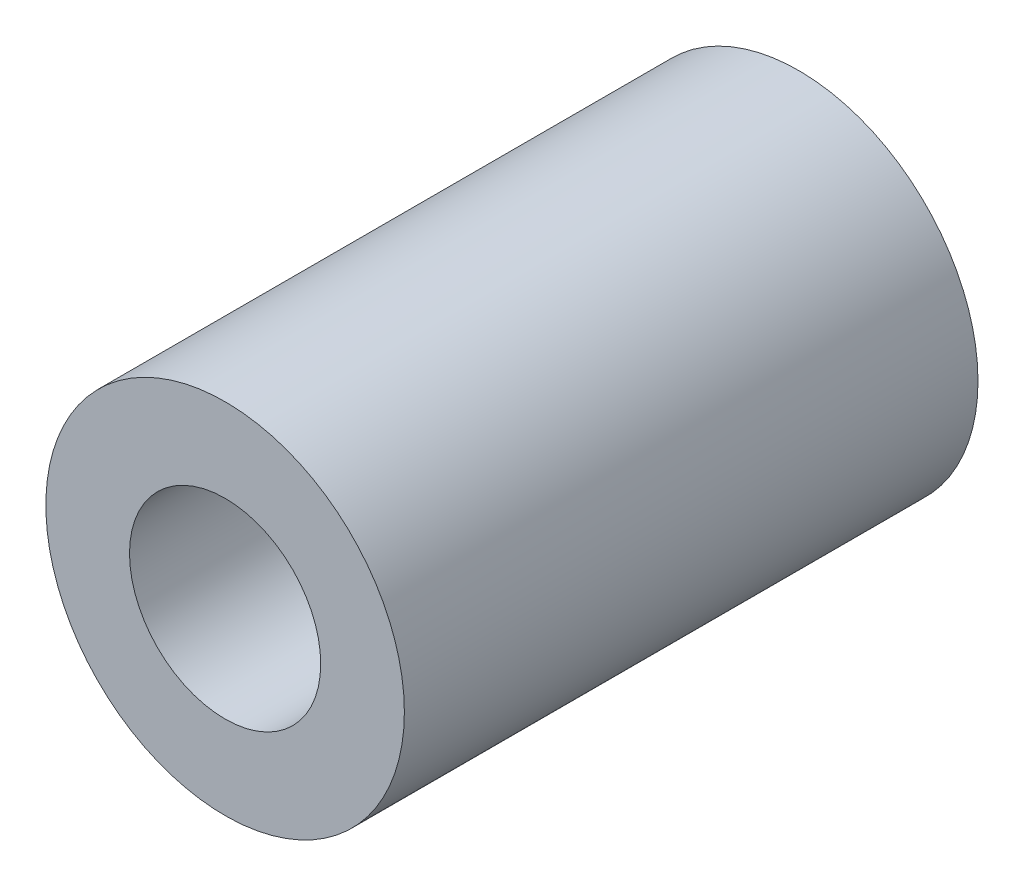
SolidWorks part; units mm, degrees
material "Liga de aço"
ref_plane "Plano frontal" through (0, 0, 0) normal (0, 0, 1) x (1, 0, 0)
ref_plane "Plano superior" through (0, 0, 0) normal (0, 1, 0) x (1, 0, 0)
ref_plane "Plano direito" through (0, 0, 0) normal (1, 0, 0) x (0, 0, -1)
sketch "Esboço1" plane through (0, 0, 0) normal (0, 0, 1) x (1, 0, 0)
  circle A0 centre (0, 0) radius 4
  circle A1 centre (0, 0) radius 7.5
  dimension "D1" = 15
  dimension "D2" = 8
extrude "Ressalto-extrusão1" add sketch "Esboço1" along normal blind 24
